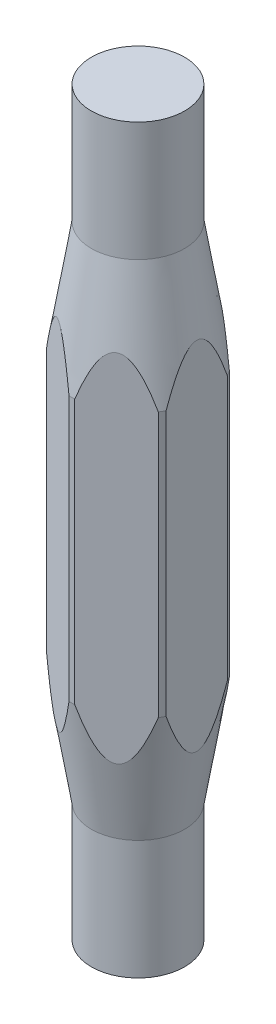
SolidWorks part; units mm, degrees
material "6061-T6 (SS)"
ref_plane "Front Plane" through (0, 0, 0) normal (0, 0, 1) x (1, 0, 0)
ref_plane "Top Plane" through (0, 0, 0) normal (0, 1, 0) x (1, 0, 0)
ref_plane "Right Plane" through (0, 0, 0) normal (1, 0, 0) x (0, 0, -1)
sketch "Sketch1" plane through (0, 0, 0) normal (0, 0, 1) x (1, 0, 0)
  line L0 (2.2371, -12.065) -> (3.175, -6.35)
  line L1 (3.175, -6.35) -> (3.175, 6.35)
  line L2 (3.175, 6.35) -> (2.2371, 12.065)
  line L3 (2.2371, 12.065) -> (2.2371, -12.065)
  line L4 (2.2371, 0) -> (3.175, 0) construction
  line L5 (0, 6.0414) -> (0, -4.6122) construction
  point P6 (1.8857, -12.1521)
  point P7 (0, 0)
  point P8 (2.2371, -12.065)
  dimension "D1" = 24.13
  dimension "D2" = 12.7
  dimension "D3" = 3.175
revolve "Revolve1" add sketch "Sketch1" angle 360 about L5
ref_plane "Plane1" through (0, 0, 3.175) normal (0, 0, 1) x (1, 0, 0)
sketch "Sketch3" plane through (0, 0, 3.175) normal (0, 0, 1) x (1, 0, 0)
  line L1 (-3.2443, -10.1093) -> (-2.8155, -10.1093)
  line L2 (-3.2443, -10.1093) -> (-3.2443, 8.7912)
  line L3 (-3.2443, 8.7912) -> (-2.8155, 8.7912)
  line L4 (-2.8155, -10.1093) -> (-2.8155, 8.7912)
extrude "Cut-Extrude1" cut sketch "Sketch3" against normal through all
pattern_circular "CirPattern1" count 6 over 360 about axis through (0, 0, 0) along (0, 1, 0) of "Cut-Extrude1"
sketch "Sketch5" plane through (0, 0, 0) normal (0, 1, 0) x (1, 0, 0)
  circle A0 centre (0, 0) radius 2.2371
  circle A1 centre (0, 0) radius 2.2371 construction
extrude "Boss-Extrude1" add sketch "Sketch5" along normal blind 17.78 and the other way blind 17.78
